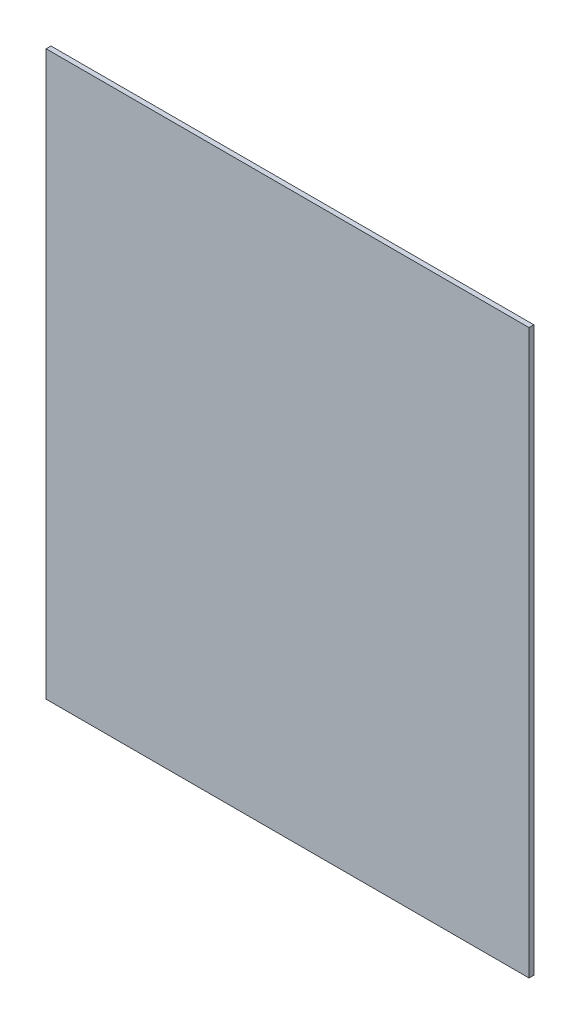
SolidWorks part; units mm, degrees
ref_plane "Plan de face" through (0, 0, 0) normal (0, 0, 1) x (1, 0, 0)
ref_plane "Plan de dessus" through (0, 0, 0) normal (0, 1, 0) x (1, 0, 0)
ref_plane "Plan de droite" through (0, 0, 0) normal (1, 0, 0) x (0, 0, -1)
sketch "Esquisse1" plane through (0, 0, 0) normal (0, 0, 1) x (1, 0, 0)
  line L1 (0, 0) -> (300, 0)
  line L2 (0, 0) -> (0, 350)
  line L3 (0, 350) -> (300, 350)
  line L4 (300, 0) -> (300, 350)
  dimension "D1" = 350
  dimension "D2" = 300
extrude "Boss.-Extru.1" add sketch "Esquisse1" along normal blind 3
